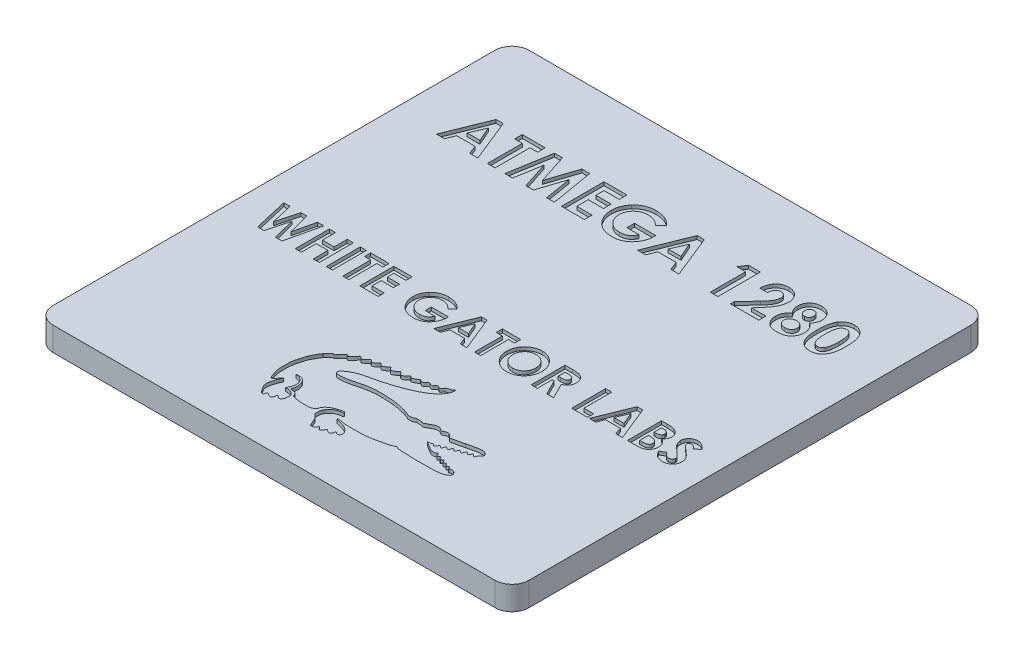
SolidWorks part; units mm, degrees
ref_plane "Front Plane" through (0, 0, 0) normal (0, 0, 1) x (1, 0, 0)
ref_plane "Top Plane" through (0, 0, 0) normal (0, 1, 0) x (1, 0, 0)
ref_plane "Right Plane" through (0, 0, 0) normal (1, 0, 0) x (0, 0, -1)
sketch "Sketch1" plane through (0, 0, 0) normal (0, 1, 0) x (1, 0, 0)
  line L0 (7, -6.5) -> (7, 6.5)
  line L1 (6.5, -7) -> (-6.5, -7)
  line L2 (6.5, 7) -> (-6.5, 7)
  line L3 (-7, -6.5) -> (-7, 6.5)
  line L4 (7, -7) -> (-7, 7) construction
  line L5 (7, 7) -> (-7, -7) construction
  arc A0 (7, 6.5) -> (6.5, 7) centre (6.5, 6.5) ccw
  arc A1 (6.5, -7) -> (7, -6.5) centre (6.5, -6.5) ccw
  arc A2 (-6.5, -7) -> (-7, -6.5) centre (-6.5, -6.5) cw
  arc A3 (-6.5, 7) -> (-7, 6.5) centre (-6.5, 6.5) ccw
  point P1 (0, 0)
  dimension "D3" = 0.5
  dimension "D1" = 14
  dimension "D2" = 14
extrude "Boss-Extrude1" add sketch "Sketch1" along normal blind 0.7
sketch "Sketch2" plane through (0, 0.7, 0) normal (0, 1, 0) x (1, 0, 0)
  spline S0 degree 3 poles (1.0687, -2.7326) (1.0434, -2.8041) (0.9259, -2.7867) (0.8512, -2.8664) (0.7873, -2.9441) (0.7487, -2.8992) (0.7025, -2.8733) (0.6592, -2.9265) (0.6147, -2.9888) (0.5566, -2.9455) (0.4884, -2.9261) (0.4462, -2.9871) (0.39, -3.0379) (0.3349, -3.0097) (0.2908, -2.9832) (0.2548, -3.0144) (0.2174, -3.0363) (0.1764, -3.0599) (0.1421, -3.0767) (0.115, -3.0782) (0.0918, -3.075) (0.0849, -3.0559) (0.0761, -3.0399) (0.0558, -3.0384) (0.0341, -3.0471) (0.0172, -3.0768) (-0.014, -3.1121) (-0.0521, -3.1399) (-0.0878, -3.1546) (-0.1078, -3.1548) (-0.127, -3.1485) (-0.1558, -3.1386) (-0.1663, -3.1041) (-0.1766, -3.0714) (-0.2022, -3.0687) (-0.2153, -3.0837) (-0.2395, -3.1008) (-0.2707, -3.1322) (-0.3113, -3.16) (-0.3536, -3.1788) (-0.3962, -3.1818) (-0.4255, -3.1548) (-0.4355, -3.131) (-0.4391, -3.1098) (-0.4542, -3.1058) (-0.4712, -3.1053) (-0.4833, -3.1204) (-0.5251, -3.1572) (-0.5701, -3.1912) (-0.6305, -3.2144) (-0.6564, -3.1972) (-0.6721, -3.1738) (-0.6885, -3.1548) (-0.7136, -3.145) (-0.7354, -3.1634) (-0.7601, -3.1922) (-0.7916, -3.2248) (-0.8301, -3.249) (-0.8621, -3.2585) (-0.8931, -3.2516) (-0.9099, -3.2296) (-0.9238, -3.2012) (-0.9484, -3.2093) (-0.9684, -3.2138) (-0.9843, -3.2318) (-1.0225, -3.2732) (-1.0594, -3.3096) (-1.1036, -3.3373) (-1.1157, -3.3314) (-1.1273, -3.322) (-1.1383, -3.3079) (-1.1508, -3.2941) (-1.1628, -3.279) (-1.1837, -3.2738) (-1.2006, -3.287) (-1.2235, -3.313) (-1.2567, -3.3552) (-1.3036, -3.4059) (-1.3486, -3.4374) (-1.3695, -3.4646) (-1.3859, -3.4647) (-1.3835, -3.4542) (-1.3906, -3.445) (-1.393, -3.4256) (-1.4256, -3.4293) (-1.4467, -3.4478) (-1.4772, -3.4796) (-1.5178, -3.5196) (-1.5602, -3.574) (-1.5975, -3.605) (-1.6122, -3.6295) (-1.6242, -3.6278) (-1.6299, -3.6187) (-1.636, -3.6124) (-1.6424, -3.607) (-1.6514, -3.6077) (-1.6662, -3.6157) (-1.6834, -3.6397) (-1.74, -3.6786) (-1.7723, -3.7294) (-1.8022, -3.7604) knots 0 0 0 0 0.048217 0.074017 0.097146 0.105851 0.117816 0.135226 0.154495 0.169729 0.186348 0.206897 0.224495 0.242122 0.253157 0.262095 0.27718 0.290164 0.300936 0.307749 0.312916 0.318201 0.323368 0.326572 0.333893 0.341326 0.35386 0.37272 0.379457 0.385348 0.388647 0.396148 0.408918 0.416225 0.422134 0.425673 0.432114 0.446566 0.4619 0.47218 0.484819 0.494044 0.502532 0.506729 0.50973 0.514353 0.519954 0.524425 0.560719 0.566271 0.575283 0.583006 0.589877 0.595845 0.602708 0.610899 0.62798 0.639327 0.648132 0.654753 0.663856 0.670956 0.676434 0.682355 0.688018 0.695368 0.72906 0.732221 0.735224 0.739169 0.744684 0.749827 0.75449 0.760478 0.76498 0.771213 0.789299 0.808978 0.827723 0.834537 0.836225 0.838451 0.841007 0.84604 0.851443 0.862598 0.869814 0.88748 0.909678 0.925709 0.928453 0.931263 0.933789 0.936972 0.93865 0.940357 0.943965 0.952208 0.964086 1 1 1 1
  spline S1 degree 3 poles (-1.8022, -3.7604) (-1.8119, -3.7815) (-1.8425, -3.8155) (-1.8763, -3.8759) (-1.9149, -3.9428) (-1.9581, -4.0249) (-1.9912, -4.1196) (-2.018, -4.2177) (-2.0405, -4.3006) (-2.058, -4.3814) (-2.0696, -4.4724) (-2.0718, -4.5968) (-2.0736, -4.7285) (-2.0603, -4.859) (-2.0287, -4.9693) (-1.989, -5.0589) (-1.9695, -5.119) (-1.9441, -5.1391) (-1.9254, -5.131) (-1.9019, -5.1281) (-1.8719, -5.1007) (-1.8489, -5.0606) (-1.829, -5.0139) (-1.8034, -4.9861) (-1.7844, -4.969) (-1.7749, -4.9573) (-1.7627, -4.9571) (-1.7645, -4.9728) (-1.7764, -4.9835) (-1.786, -5.008) (-1.803, -5.0387) (-1.8218, -5.091) (-1.8409, -5.1511) (-1.8572, -5.2104) (-1.8629, -5.2623) (-1.8765, -5.3038) (-1.8748, -5.3465) (-1.8769, -5.3884) (-1.8628, -5.4326) (-1.8432, -5.4724) (-1.8228, -5.5152) (-1.7921, -5.5572) (-1.7558, -5.599) (-1.73, -5.6425) (-1.6971, -5.6673) (-1.6656, -5.671) (-1.6452, -5.6536) (-1.6388, -5.632) (-1.6393, -5.6129) (-1.6405, -5.5986) (-1.6355, -5.5857) (-1.6268, -5.5768) (-1.6148, -5.5718) (-1.6012, -5.5738) (-1.5836, -5.5756) (-1.573, -5.5912) (-1.5523, -5.5987) (-1.5356, -5.6161) (-1.5084, -5.6321) (-1.4705, -5.6435) (-1.4507, -5.6138) (-1.4302, -5.5943) (-1.425, -5.5639) (-1.4247, -5.5374) (-1.4235, -5.5119) (-1.4077, -5.4985) (-1.3896, -5.4905) (-1.3723, -5.5027) (-1.3504, -5.5142) (-1.3319, -5.5329) (-1.306, -5.5485) (-1.2677, -5.5356) (-1.244, -5.4958) (-1.2136, -5.4362) (-1.2208, -5.3695) (-1.2111, -5.3092) (-1.2279, -5.2722) (-1.2477, -5.2432) (-1.2751, -5.2192) (-1.3068, -5.2063) (-1.3373, -5.1885) (-1.3698, -5.1793) (-1.4191, -5.172) (-1.4485, -5.1716) (-1.4836, -5.174) (-1.4814, -5.1614) (-1.4701, -5.1407) (-1.4472, -5.1016) (-1.4275, -5.0454) (-1.4114, -4.9836) (-1.4051, -4.9093) (-1.4157, -4.8395) (-1.4547, -4.7825) (-1.4968, -4.7452) (-1.5402, -4.713) (-1.5886, -4.6971) (-1.6317, -4.6881) (-1.6558, -4.6846) (-1.6704, -4.6797) (-1.6148, -4.6661) (-1.5922, -4.6798) (-1.5406, -4.6728) (-1.5131, -4.6813) (-1.4863, -4.6915) (-1.4578, -4.7059) (-1.4342, -4.7303) (-1.4065, -4.7588) (-1.3839, -4.7954) (-1.3665, -4.8326) (-1.357, -4.8701) (-1.3481, -4.9094) (-1.3484, -4.9547) (-1.3485, -5.0019) (-1.3607, -5.0528) (-1.3618, -5.0923) (-1.382, -5.1243) (-1.3714, -5.1335) (-1.3579, -5.135) (-1.3344, -5.1404) (-1.3016, -5.1406) (-1.2698, -5.152) (-1.2397, -5.1569) (-1.1877, -5.1812) (-1.1707, -5.2307) (-1.1638, -5.2726) (-1.1552, -5.2736) (-1.1286, -5.2797) (-1.0923, -5.2912) (-1.0507, -5.3) (-1.0087, -5.307) (-0.9633, -5.3128) (-0.9165, -5.3231) (-0.8788, -5.3269) (-0.839, -5.3244) (-0.789, -5.3237) (-0.7354, -5.3231) (-0.6814, -5.3241) (-0.6318, -5.3264) (-0.5833, -5.3073) (-0.5341, -5.2863) (-0.4809, -5.2338) (-0.4723, -5.1778) (-0.4534, -5.1474) knots 0 0 0 0 0.011292 0.0223 0.033937 0.049308 0.06781 0.083097 0.099329 0.110042 0.123747 0.144309 0.171172 0.188484 0.208653 0.227112 0.237112 0.238855 0.242007 0.245967 0.250578 0.261005 0.268815 0.27527 0.279338 0.281421 0.282634 0.283842 0.287544 0.290725 0.296449 0.304901 0.317893 0.327543 0.335024 0.343551 0.348647 0.355939 0.36406 0.371053 0.377797 0.387292 0.3965 0.405032 0.411989 0.416065 0.419424 0.424193 0.426622 0.428837 0.431213 0.433133 0.434832 0.437334 0.43983 0.443124 0.44581 0.450442 0.454609 0.461905 0.465987 0.470748 0.475758 0.480319 0.484232 0.487455 0.490017 0.493236 0.496918 0.50239 0.506103 0.511016 0.520157 0.528136 0.543489 0.552071 0.557352 0.562929 0.569365 0.574847 0.579708 0.586636 0.591433 0.603611 0.604429 0.605144 0.608671 0.61724 0.626494 0.638192 0.648395 0.663163 0.671649 0.681816 0.690801 0.69782 0.706956 0.711272 0.711751 0.712906 0.728184 0.7329 0.736849 0.742242 0.747053 0.752347 0.758799 0.766576 0.773328 0.778941 0.785536 0.79309 0.801066 0.808798 0.818211 0.822204 0.823125 0.824553 0.828768 0.835042 0.840421 0.845231 0.850035 0.867854 0.868398 0.869422 0.871421 0.882677 0.887419 0.892446 0.903561 0.909938 0.916008 0.92211 0.929499 0.940595 0.948448 0.956154 0.964623 0.973682 0.982416 1 1 1 1
  spline S2 degree 3 poles (-0.4534, -5.1474) (-0.4448, -5.1381) (-0.4304, -5.1138) (-0.3903, -5.0749) (-0.3371, -5.0363) (-0.2743, -4.9961) (-0.2038, -4.9733) (-0.1398, -4.9528) (-0.0914, -4.9331) (-0.0567, -4.9325) (-0.0308, -4.9244) (-0.0048, -4.9199) (0.0129, -4.9334) (0.0139, -4.9517) (0.0028, -4.9681) (-0.0269, -4.9739) (-0.0612, -4.9712) (-0.1002, -4.9839) (-0.1321, -4.9906) (-0.1871, -5.0097) (-0.2484, -5.0399) (-0.289, -5.087) (-0.3187, -5.1157) (-0.3467, -5.1536) (-0.3715, -5.2058) (-0.3942, -5.2562) (-0.3898, -5.2937) (-0.394, -5.3274) (-0.3912, -5.3622) (-0.3956, -5.4044) (-0.3696, -5.4306) (-0.3433, -5.4543) (-0.3174, -5.4817) (-0.2866, -5.5119) (-0.2594, -5.5419) (-0.2468, -5.5737) (-0.2375, -5.6045) (-0.2225, -5.6399) (-0.2011, -5.6806) (-0.1823, -5.7241) (-0.1672, -5.7604) (-0.1408, -5.7711) (-0.1204, -5.769) (-0.0956, -5.7728) (-0.0669, -5.7579) (-0.0393, -5.7348) (-0.0161, -5.7088) (-0.0098, -5.6849) (-0.001, -5.6721) (0.0129, -5.6713) (0.0249, -5.6884) (0.038, -5.7082) (0.0577, -5.7307) (0.0754, -5.7491) (0.1058, -5.7538) (0.1277, -5.7278) (0.15, -5.7023) (0.1617, -5.6717) (0.1782, -5.6487) (0.1771, -5.6246) (0.1964, -5.6171) (0.2057, -5.6363) (0.225, -5.6501) (0.2493, -5.6675) (0.2816, -5.6825) (0.3311, -5.6866) (0.3631, -5.6387) (0.3683, -5.6033) (0.3673, -5.5798) (0.3743, -5.5674) (0.3895, -5.5519) (0.4121, -5.5662) (0.425, -5.5833) (0.446, -5.5944) (0.4762, -5.6079) (0.5155, -5.5776) (0.559, -5.4889) (0.4853, -5.3976) (0.4489, -5.366) knots 0 0 0 0 0.013276 0.02943 0.058363 0.082476 0.107406 0.135768 0.153618 0.161689 0.171706 0.182591 0.187314 0.193219 0.199941 0.206264 0.223753 0.236038 0.248874 0.25808 0.297357 0.318574 0.322951 0.340866 0.367576 0.384252 0.397411 0.406423 0.419884 0.434504 0.448292 0.455948 0.472233 0.48765 0.501621 0.514266 0.523128 0.535517 0.554694 0.571193 0.586429 0.593101 0.599506 0.607865 0.618812 0.631781 0.646414 0.653923 0.657826 0.661848 0.666147 0.678355 0.687637 0.697562 0.704452 0.717194 0.729381 0.74086 0.751176 0.758667 0.763452 0.767118 0.778224 0.788973 0.798202 0.81609 0.83498 0.851289 0.854121 0.859303 0.865993 0.873735 0.882606 0.889168 0.898502 0.91523 0.933533 1 1 1 1
  spline S3 degree 3 poles (0.4489, -5.366) (0.4198, -5.3433) (0.3648, -5.31) (0.2811, -5.2736) (0.2092, -5.2571) (0.1459, -5.2397) (0.1036, -5.2338) (0.0718, -5.2255) (0.066, -5.1991) (0.0923, -5.1883) (0.1149, -5.1966) (0.1545, -5.2026) (0.2056, -5.2164) (0.2757, -5.2234) (0.3485, -5.235) (0.4543, -5.2379) (0.6358, -5.2346) (0.9189, -5.2357) (1.2744, -5.1623) (1.5302, -5.1079) (1.653, -5.0411) (1.6668, -5.0439) (1.6878, -5.057) (1.7258, -5.0804) (1.7725, -5.0706) (1.8179, -5.0883) (1.8632, -5.0829) (1.929, -5.0836) (2.0002, -5.0918) (2.0844, -5.0915) (2.156, -5.0903) (2.2351, -5.1008) (2.3283, -5.0967) (2.4826, -5.0991) (2.6338, -5.0964) (2.772, -5.0999) (2.897, -5.086) (2.9954, -5.0747) (3.0599, -5.0497) knots 0 0 0 0 0.031948 0.05562 0.078812 0.095961 0.112076 0.116762 0.123004 0.129426 0.136592 0.143897 0.164038 0.18245 0.204827 0.227975 0.274131 0.362396 0.472777 0.587782 0.58911 0.591037 0.599391 0.610848 0.628309 0.637774 0.65228 0.66699 0.695046 0.714252 0.739998 0.757024 0.783309 0.820706 0.890915 0.91456 0.940428 1 1 1 1
  spline S4 degree 3 poles (3.0599, -5.0497) (3.0968, -5.0401) (3.1405, -5.0131) (3.1866, -4.965) (3.1861, -4.9337) (3.1877, -4.9113) (3.1749, -4.8851) (3.1527, -4.857) (3.1162, -4.8315) (3.0742, -4.8211) (3.0329, -4.8211) (3.0053, -4.8272) (2.9956, -4.8534) (2.9896, -4.8477) (2.982, -4.8518) (2.9811, -4.84) (2.9729, -4.8345) (2.9685, -4.8211) (2.9593, -4.8063) (2.9499, -4.7905) (2.9386, -4.7797) (2.9275, -4.7791) (2.9182, -4.7805) (2.9103, -4.7864) (2.9035, -4.7947) (2.892, -4.7967) (2.8855, -4.8072) (2.8736, -4.8062) (2.861, -4.8102) (2.8548, -4.7966) (2.8475, -4.7872) (2.841, -4.7771) (2.8349, -4.7673) (2.8285, -4.7585) (2.8238, -4.7448) (2.8077, -4.7493) (2.7959, -4.7466) (2.7818, -4.7505) (2.7691, -4.7573) (2.7552, -4.7677) (2.7436, -4.7654) (2.7349, -4.767) (2.7302, -4.7577) (2.725, -4.7466) (2.7149, -4.729) (2.703, -4.7113) (2.6887, -4.6849) (2.6574, -4.7033) (2.6436, -4.7141) (2.6275, -4.7246) knots 0 0 0 0 0.116546 0.171979 0.193509 0.214321 0.242769 0.28328 0.328295 0.381564 0.418486 0.458732 0.472205 0.475171 0.481197 0.492392 0.499562 0.512518 0.53505 0.555738 0.571406 0.581908 0.589881 0.601112 0.612531 0.622685 0.63654 0.645931 0.659362 0.672182 0.686145 0.69901 0.71008 0.722753 0.735214 0.748491 0.766903 0.774853 0.793955 0.813799 0.825742 0.830967 0.839633 0.853705 0.872929 0.901651 0.928936 0.946032 1 1 1 1
  spline S5 degree 3 poles (2.6275, -4.7246) (2.6216, -4.725) (2.6122, -4.7315) (2.5993, -4.7243) (2.5945, -4.7134) (2.5839, -4.6928) (2.577, -4.6709) (2.5616, -4.6541) (2.5495, -4.6538) (2.5389, -4.66) (2.5255, -4.6677) (2.5105, -4.6763) (2.4974, -4.6829) (2.483, -4.6852) (2.4741, -4.6723) (2.4655, -4.6525) (2.4563, -4.6318) (2.4483, -4.6121) (2.4351, -4.6024) (2.4247, -4.609) (2.4134, -4.6148) (2.3939, -4.6268) (2.3579, -4.6369) (2.3134, -4.6372) (2.2718, -4.6375) (2.2315, -4.6261) (2.1934, -4.6032) (2.1435, -4.5738) (2.0969, -4.5441) (2.0331, -4.5043) (2.008, -4.49) (1.9651, -4.4579) (1.9715, -4.4588) (1.9781, -4.4584) (2.0132, -4.4584) (2.0625, -4.4697) (2.0916, -4.4352) (2.1106, -4.4286) (2.1229, -4.4351) (2.1324, -4.4455) (2.1454, -4.4544) (2.1567, -4.4649) (2.1676, -4.475) (2.182, -4.4779) (2.1962, -4.4722) (2.2126, -4.4577) (2.2276, -4.4249) (2.2419, -4.3995) (2.2566, -4.3729) (2.272, -4.3799) (2.2857, -4.3966) (2.3072, -4.4112) (2.3305, -4.4228) (2.3496, -4.414) (2.3564, -4.3941) (2.3648, -4.3737) (2.3677, -4.3519) (2.3713, -4.3334) (2.3839, -4.3196) (2.4039, -4.3214) (2.4221, -4.333) (2.4397, -4.3489) (2.4577, -4.3596) (2.4745, -4.3744) (2.4978, -4.3549) (2.4959, -4.3345) (2.5009, -4.3214) knots 0 0 0 0 0.01228 0.017915 0.026275 0.034934 0.063098 0.070685 0.076795 0.084706 0.094302 0.106898 0.118255 0.123209 0.133348 0.143983 0.166978 0.17609 0.186449 0.192439 0.198312 0.211604 0.236514 0.269678 0.29806 0.316842 0.350191 0.384057 0.429 0.460133 0.521155 0.52446 0.526804 0.529734 0.538915 0.592764 0.614566 0.621436 0.629926 0.639335 0.649221 0.660155 0.669493 0.677461 0.68716 0.698241 0.719488 0.754519 0.762314 0.769012 0.781857 0.805945 0.819101 0.829391 0.842334 0.858062 0.872694 0.884767 0.894389 0.905805 0.919872 0.936456 0.950947 0.962907 0.972927 1 1 1 1
  spline S6 degree 3 poles (2.5009, -4.3214) (2.5062, -4.305) (2.5054, -4.2763) (2.5341, -4.2601) (2.5532, -4.267) (2.571, -4.2822) (2.5896, -4.2958) (2.6127, -4.3171) (2.639, -4.2835) (2.6438, -4.2501) (2.6584, -4.221) (2.6777, -4.2012) (2.6934, -4.2171) (2.7131, -4.2241) (2.7284, -4.2411) (2.75, -4.2538) (2.7785, -4.2442) (2.7828, -4.2153) (2.7959, -4.1872) (2.8087, -4.166) (2.8263, -4.1461) (2.8461, -4.153) (2.859, -4.1694) (2.8744, -4.1864) (2.9017, -4.2062) (2.9344, -4.1685) (2.9439, -4.1348) (2.9626, -4.1077) (2.9811, -4.1058) (2.9899, -4.1189) (3.0055, -4.1288) (3.0181, -4.1452) (3.033, -4.1603) (3.0553, -4.158) (3.0733, -4.1316) (3.0777, -4.1017) (3.0829, -4.0727) (3.1039, -4.0582) (3.1339, -4.0484) (3.1682, -4.0102) (3.1658, -3.9539) (3.1348, -3.9157) (3.0979, -3.893) (3.0573, -3.8787) (3.0194, -3.8808) (2.9828, -3.8803) (2.9497, -3.8803) (2.9119, -3.8826) (2.878, -3.8909) (2.8418, -3.8979) (2.8067, -3.9082) (2.7681, -3.9155) (2.7291, -3.9211) (2.6926, -3.9331) (2.6478, -3.942) (2.6153, -3.9535) (2.593, -3.9578) knots 0 0 0 0 0.032452 0.043005 0.053246 0.066769 0.084815 0.098004 0.11284 0.145121 0.162081 0.173877 0.18503 0.195112 0.212343 0.225207 0.237914 0.259139 0.2723 0.29408 0.30574 0.314199 0.327607 0.342984 0.357158 0.380044 0.412428 0.428075 0.433327 0.443081 0.453195 0.466737 0.480816 0.487976 0.504123 0.532443 0.544592 0.554196 0.576223 0.601695 0.640749 0.665285 0.688092 0.718331 0.741128 0.755919 0.784293 0.800792 0.82413 0.846863 0.867366 0.889975 0.917733 0.938105 0.959048 1 1 1 1
  spline S7 degree 3 poles (2.593, -3.9578) (2.5703, -3.9617) (2.535, -3.9716) (2.4878, -3.982) (2.4513, -3.9892) (2.4146, -3.9975) (2.3764, -4.0072) (2.3374, -4.0153) (2.301, -4.0226) (2.2679, -4.0336) (2.2381, -4.0406) (2.2178, -4.0497) (2.2028, -4.0491) (2.1972, -4.0408) (2.1887, -4.0269) (2.1789, -4.0083) (2.1553, -3.9862) (2.1269, -3.9631) (2.0942, -3.9388) (2.0528, -3.9375) (2.0183, -3.9347) (1.9791, -3.9502) (1.9554, -3.9721) (1.9214, -3.9793) (1.892, -3.981) (1.8641, -3.9641) (1.8467, -3.9483) (1.8137, -3.9269) (1.7492, -3.9123) (1.6719, -3.9312) (1.6121, -3.9648) (1.5654, -3.9921) (1.5181, -4.0179) (1.4729, -4.0363) (1.4405, -4.0582) (1.3984, -4.057) (1.3611, -4.0357) (1.3005, -4.0365) (1.2616, -4.0336) (1.2353, -4.0358) knots 0 0 0 0 0.047002 0.074581 0.098698 0.122868 0.151468 0.179139 0.204125 0.22703 0.250435 0.266286 0.272442 0.278681 0.285282 0.306306 0.320615 0.350899 0.38222 0.399602 0.434255 0.451623 0.484206 0.497344 0.522159 0.541774 0.561793 0.570227 0.621862 0.69065 0.727534 0.761683 0.801147 0.83719 0.861929 0.878108 0.919976 0.946367 1 1 1 1
  spline S8 degree 3 poles (1.2353, -4.0358) (1.2195, -4.035) (1.1903, -4.0524) (1.1414, -4.075) (1.0799, -4.0782) (1.015, -4.0798) (0.9502, -4.04) (0.9009, -4.0254) (0.8699, -4.0146) knots 0 0 0 0 0.122508 0.251505 0.420804 0.597875 0.74414 1 1 1 1
  spline S9 degree 3 poles (0.8699, -4.0146) (0.8181, -3.9941) (0.7504, -3.988) (0.6729, -3.9629) (0.634, -3.9531) (0.5914, -3.9476) (0.5471, -3.939) (0.4995, -3.9301) (0.428, -3.9196) (0.3303, -3.9153) (0.1842, -3.9031) (0.0352, -3.9113) (-0.0902, -3.9018) (-0.1761, -3.9173) (-0.2457, -3.9222) (-0.3247, -3.9316) (-0.3937, -3.9473) (-0.4507, -3.9633) (-0.501, -3.9743) (-0.5557, -3.9912) (-0.6327, -4.0078) (-0.7255, -4.0348) (-0.8081, -4.0489) (-0.9061, -4.0658) (-0.9848, -4.0663) (-1.0668, -4.0727) (-1.1052, -4.0532) (-1.1308, -4.0267) (-1.1342, -3.9903) (-1.1096, -3.9563) (-1.0572, -3.9036) (-0.9803, -3.8447) (-0.8842, -3.8028) (-0.8042, -3.7591) (-0.7268, -3.7367) (-0.6536, -3.7123) (-0.5713, -3.6959) (-0.4764, -3.6728) (-0.3701, -3.652) (-0.2727, -3.6256) (-0.1675, -3.5932) (-0.0527, -3.5659) (0.063, -3.5277) (0.1745, -3.4909) (0.3293, -3.4317) (0.5158, -3.3556) (0.7173, -3.2459) (0.89, -3.1301) (1.0108, -2.9952) (1.0755, -2.8592) (1.0954, -2.7699) (1.0687, -2.7326) knots 0 0 0 0 0.034896 0.042335 0.051393 0.060137 0.069415 0.079869 0.090743 0.114971 0.14154 0.1831 0.209109 0.220295 0.237991 0.25316 0.27044 0.282575 0.290489 0.302931 0.318711 0.340126 0.363845 0.371564 0.402788 0.413927 0.422227 0.429111 0.436434 0.442975 0.454753 0.483686 0.503113 0.520859 0.54098 0.553763 0.569549 0.593837 0.615431 0.637896 0.657454 0.684852 0.7123 0.734326 0.758932 0.816879 0.86128 0.903494 0.947905 0.972512 1 1 1 1
  text T0 "<b>ATMEGA 1280</b>\r\n\r\n" font "Century Gothic" height 1.25
  text T1 "<b>WHITE GATOR LABS</b>" font "Century Gothic" height 1
extrude "Cut-Extrude1" cut sketch "Sketch2" against normal blind 0.1
